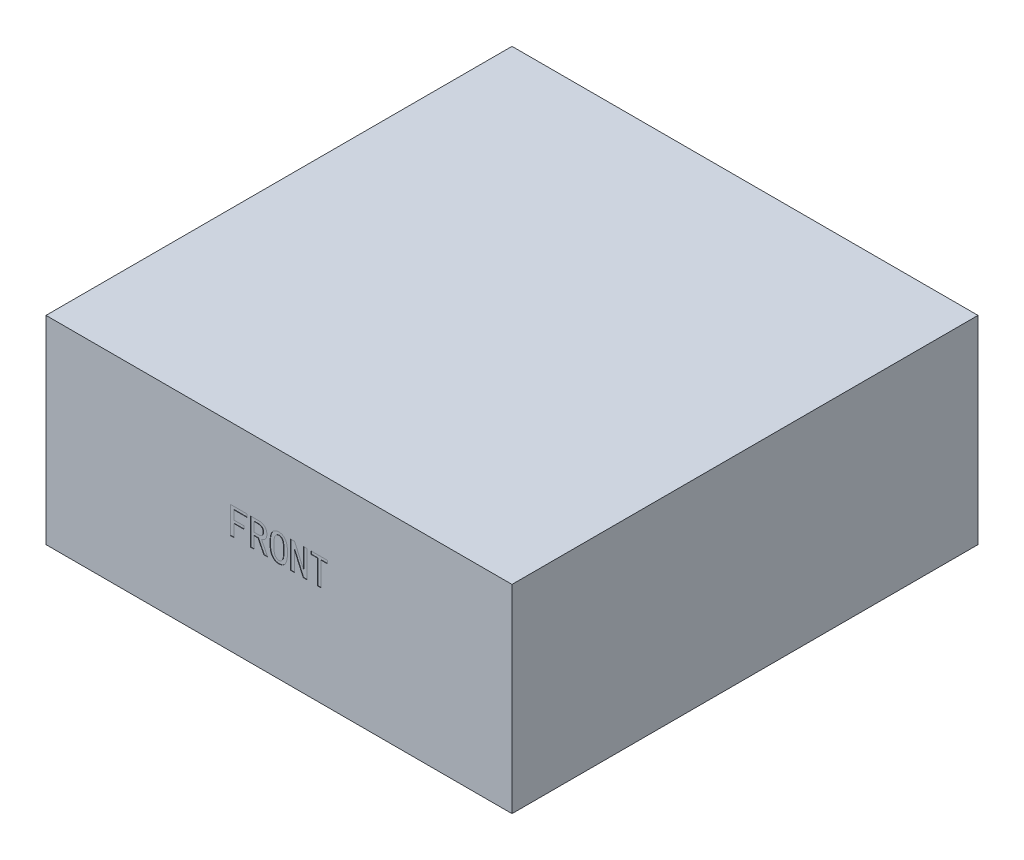
SolidWorks part; units mm, degrees
ref_plane "前视基准面" through (0, 0, 0) normal (0, 0, 1) x (1, 0, 0)
ref_plane "上视基准面" through (0, 0, 0) normal (0, 1, 0) x (1, 0, 0)
ref_plane "右视基准面" through (0, 0, 0) normal (1, 0, 0) x (0, 0, -1)
sketch "Sketch1" plane through (0, 0, 0) normal (0, 1, 0) x (1, 0, 0)
  line L1 (-57.5, 57.5) -> (57.5, 57.5)
  line L2 (-57.5, 57.5) -> (-57.5, -57.5)
  line L3 (-57.5, -57.5) -> (57.5, -57.5)
  line L4 (57.5, 57.5) -> (57.5, -57.5)
  line L5 (-57.5, 57.5) -> (57.5, -57.5) construction
  line L6 (-57.5, -57.5) -> (57.5, 57.5) construction
  point P0 (0, 0)
  dimension "D1" = 115
  dimension "D2" = 115
extrude "Boss-Extrude1" add sketch "Sketch1" along normal blind 49
sketch "Sketch2" plane through (0, 0, 57.5) normal (0, 0, 1) x (1, 0, 0)
  line L0 (-57.5, 24.5) -> (57.5, 24.5) construction
  line L1 (-57.5, 49) -> (-57.5, 0) construction
  line L2 (57.5, 49) -> (57.5, 0) construction
  text T0 "FRONT" font "黑体" height in points 22
extrude "Cut-Extrude1" cut sketch "Sketch2" against normal blind 0.1
sketch "Sketch3" plane through (0, 0, 0) normal (0, -1, 0) x (1, 0, 0)
  line L0 (-15, 57.5) -> (-15, -57.5) construction
  line L3 (-57.5, 57.5) -> (57.5, 57.5) construction
  line L4 (57.5, -57.5) -> (-57.5, -57.5) construction
  line L5 (-15, -42.5) -> (-15, 42.5) construction
  line L6 (-57.5, -57.5) -> (-57.5, 57.5) construction
  circle A0 centre (-15, 42.5) radius 1.5
  circle A1 centre (-15, -42.5) radius 1.5
  point P9 (-15, 0)
  dimension "D3" = 3
  dimension "D4" = 3
  dimension "D1" = 85
  dimension "D2" = 42.5
extrude "Cut-Extrude2" cut sketch "Sketch3" against normal blind 10
